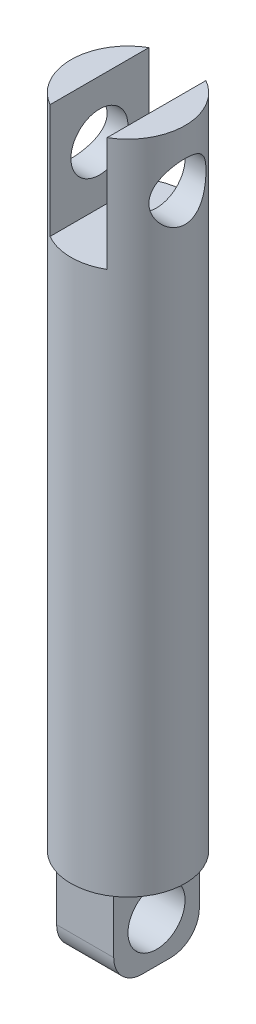
SolidWorks part; units mm, degrees
ref_plane "Front Plane" through (0, 0, 0) normal (0, 0, 1) x (1, 0, 0)
ref_plane "Top Plane" through (0, 0, 0) normal (0, 1, 0) x (1, 0, 0)
ref_plane "Right Plane" through (0, 0, 0) normal (1, 0, 0) x (0, 0, -1)
sketch "Sketch1" plane through (0, 0, 0) normal (0, 1, 0) x (1, 0, 0)
  circle A0 centre (0, 0) radius 10
  dimension "D1" = 20
extrude "Boss-Extrude1" add sketch "Sketch1" along normal blind 95
sketch "Sketch4" plane through (0, 0, 0) normal (0, -1, 0) x (1, 0, 0)
  line L1 (5, 7.5) -> (-5, 7.5)
  line L2 (5, 7.5) -> (5, -7.5)
  line L3 (5, -7.5) -> (-5, -7.5)
  line L4 (-5, 7.5) -> (-5, -7.5)
  line L5 (5, 7.5) -> (-5, -7.5) construction
  line L6 (5, -7.5) -> (-5, 7.5) construction
  point P0 (0, 0)
  dimension "D1" = 10
  dimension "D2" = 15
extrude "Boss-Extrude3" add sketch "Sketch4" along normal blind 15
sketch "Sketch5" plane through (-5, 0, 0) normal (-1, 0, 0) x (0, 0, 1)
  line L0 (7.5, -15) -> (-7.5, -15) construction
  circle A0 centre (0, -7.5) radius 5
  dimension "D1" = 10
  dimension "D2" = 7.5
extrude "Cut-Extrude2" cut sketch "Sketch5" against normal blind 15
fillet "Fillet1" radius 5 2 edges at (0, -15, -7.5) (0, -15, 7.5)
sketch "Sketch9" plane through (0, 95, 0) normal (0, 1, 0) x (1, 0, 0)
  circle A0 centre (0, 0) radius 10
extrude "Boss-Extrude4" add sketch "Sketch9" along normal blind 20
sketch "Sketch10" plane through (0, 115, 0) normal (0, 1, 0) x (1, 0, 0)
  line L1 (-5, 18.1369) -> (5, 18.1369)
  line L2 (-5, 18.1369) -> (-5, -18.1369)
  line L3 (-5, -18.1369) -> (5, -18.1369)
  line L4 (5, 18.1369) -> (5, -18.1369)
  line L5 (-5, 18.1369) -> (5, -18.1369) construction
  line L6 (-5, -18.1369) -> (5, 18.1369) construction
  point P0 (0, 0)
  dimension "D1" = 10
extrude "Cut-Extrude4" cut sketch "Sketch10" against normal blind 20
sketch "Sketch12" plane through (0, 0, 0) normal (1, 0, 0) x (0, 0, -1)
  circle A0 centre (0, 105) radius 5
  dimension "D1" = 105
  dimension "D2" = 10
extrude "Cut-Extrude5" cut sketch "Sketch12" against normal through all and the other way through all
